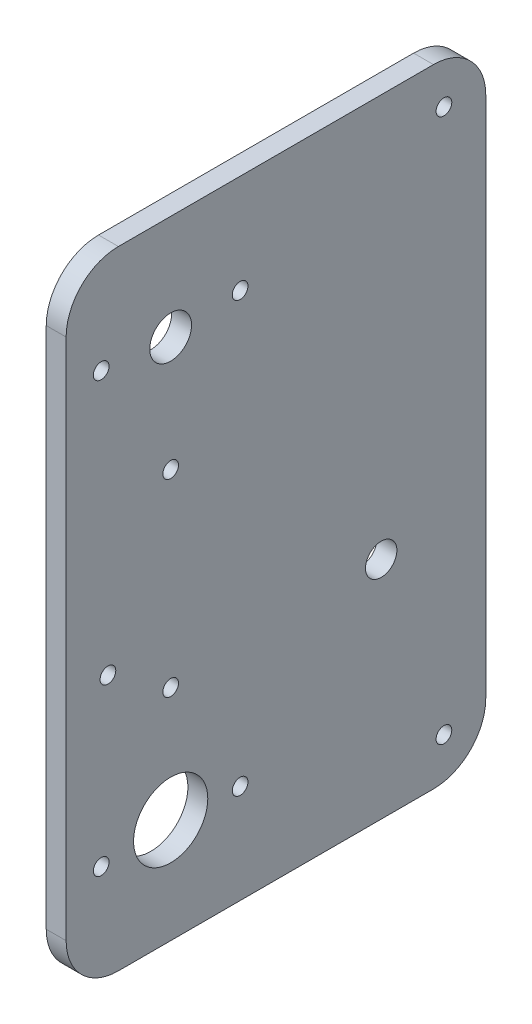
SolidWorks part; units mm, degrees
ref_plane "Front Plane" through (0, 0, 0) normal (0, 0, 1) x (1, 0, 0)
ref_plane "Top Plane" through (0, 0, 0) normal (0, 1, 0) x (1, 0, 0)
ref_plane "Right Plane" through (0, 0, 0) normal (1, 0, 0) x (0, 0, -1)
sketch "Sketch1" plane through (0, 0, 0) normal (1, 0, 0) x (0, 0, -1)
  line L0 (2.0601, -18.4136) -> (2.0601, -98.4136) construction
  line L5 (2.0601, -75.3642) -> (42.3302, -75.3642) construction
  line L6 (-17.9399, -68.4136) -> (-9.9399, -68.4136) construction
  line L7 (-17.9399, 1.5864) -> (62.3302, 1.5864)
  line L8 (-17.9399, 1.5864) -> (-17.9399, -118.4136)
  line L9 (-17.9399, -118.4136) -> (62.3302, -118.4136)
  line L10 (62.3302, 1.5864) -> (62.3302, -118.4136)
  line L11 (2.0601, -76.4729) -> (-11.2254, -99.4839) construction
  line L12 (-11.2254, -99.4839) -> (15.3455, -99.4839) construction
  line L13 (-17.9399, -58.4136) -> (62.3302, -58.4136) construction
  line L14 (15.3455, -99.4839) -> (2.0601, -76.4729) construction
  line L15 (2.0601, -98.4136) -> (2.0601, -99.4839) construction
  line L16 (-11.2254, -99.4839) -> (-17.9399, -99.4839) construction
  line L17 (2.0601, -40.3542) -> (15.3455, -17.3432) construction
  line L18 (15.3455, -17.3432) -> (-11.2254, -17.3432) construction
  line L19 (-11.2254, -17.3432) -> (2.0601, -40.3542) construction
  line L20 (2.0601, -18.4136) -> (2.0601, -17.3432) construction
  line L21 (-11.2254, -17.3432) -> (-17.9399, -17.3432) construction
  circle A0 centre (2.0601, -18.4136) radius 4
  circle A1 centre (2.0601, -98.4136) radius 7.1
  circle A3 centre (42.3302, -75.3642) radius 3
  circle A4 centre (2.0601, -98.4136) radius 17.9 construction
  circle A5 centre (2.0601, -18.4136) radius 41.25 construction
  circle A6 centre (42.3302, -75.3642) radius 28.5 construction
  circle A14 centre (54.3302, -6.4136) radius 1.5
  circle A16 centre (54.3302, -110.4136) radius 1.5
  circle A17 centre (-9.9399, -68.4136) radius 1.5
  circle A21 centre (2.0601, -76.4729) radius 1.5
  circle A25 centre (-11.2254, -99.4839) radius 1.5
  circle A26 centre (15.3455, -99.4839) radius 1.5
  circle A27 centre (15.3455, -17.3432) radius 1.5
  circle A28 centre (2.0601, -40.3542) radius 1.5
  circle A29 centre (-11.2254, -17.3432) radius 1.5
  point P5 (-13.9399, -68.4136)
  point P27 (2.0601, -98.4136)
  dimension "D2" = 8
  dimension "D3" = 14.2
  dimension "D6" = 6
  dimension "D1" = 82.5
  dimension "D4" = 35.8
  dimension "D5" = 57
  dimension "D7" = 80
  dimension "D12" = 26.5708
  dimension "D13" = 8
  dimension "D17" = 26.5708
  dimension "D18" = 26.5708
  dimension "D20" = 3
  dimension "D21" = 3
  dimension "D22" = 3
  dimension "D27" = 3
  dimension "D28" = 3
  dimension "D29" = 3
  dimension "D30" = 3
  dimension "D31" = 3
  dimension "D8" = 20
  dimension "D9" = 20
  dimension "D10" = 20
  dimension "D11" = 20
  dimension "D14" = 8
  dimension "D15" = 10
  dimension "D16" = 8
  dimension "D19" = 1.0703
  dimension "D23" = 26.5708
  dimension "D24" = 26.5708
  dimension "D25" = 26.5708
  dimension "D26" = 1.0703
extrude "Boss-Extrude1" add sketch "Sketch1" along normal blind 3.8
fillet "Fillet1" radius 10 4 edges at (1.9, 1.5864, 17.9399) (1.9, 1.5864, -62.3302) (1.9, -118.4136, -62.3302) (1.9, -118.4136, 17.9399)
